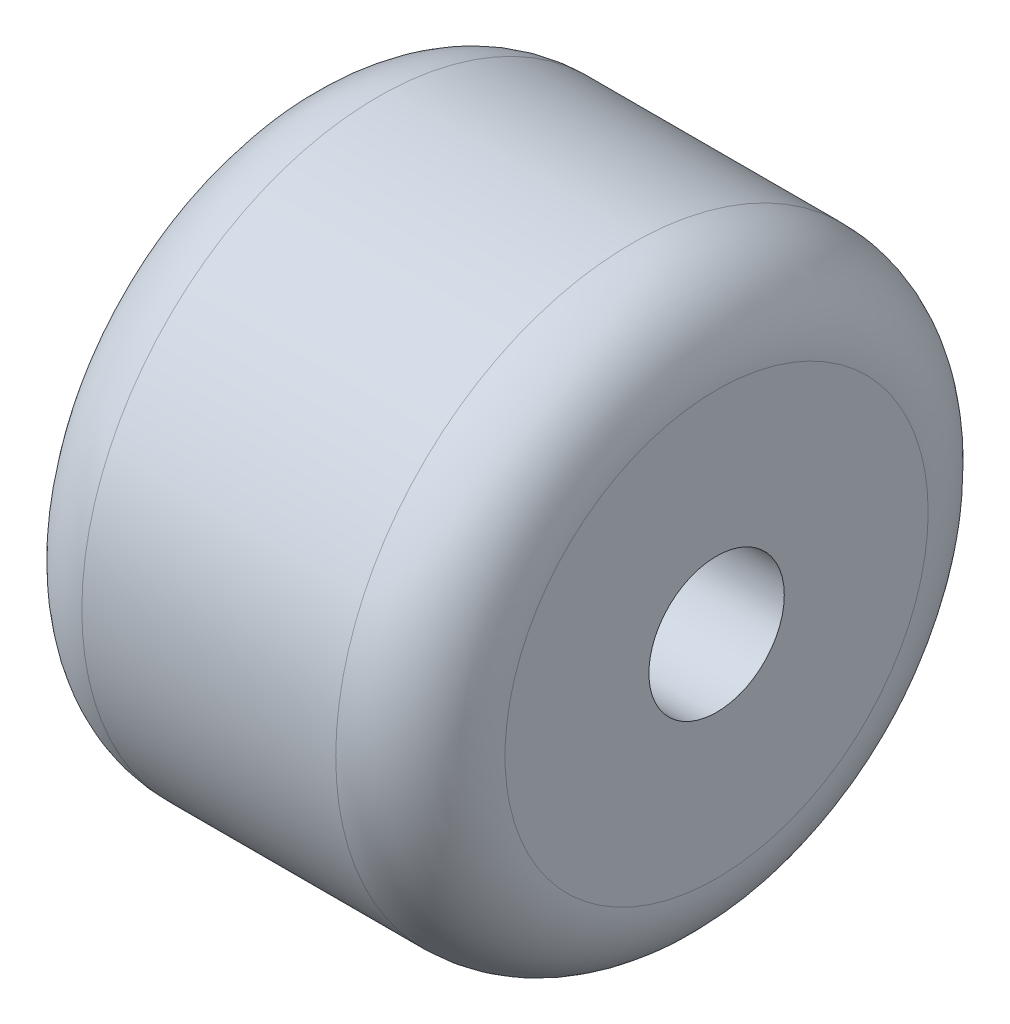
SolidWorks part; units mm, degrees
ref_plane "Plan de face" through (0, 0, 0) normal (0, 0, 1) x (1, 0, 0)
ref_plane "Plan de dessus" through (0, 0, 0) normal (0, 1, 0) x (1, 0, 0)
ref_plane "Plan de droite" through (0, 0, 0) normal (1, 0, 0) x (0, 0, -1)
sketch "Esquisse1" plane through (0, 0, 0) normal (1, 0, 0) x (0, 0, -1)
  circle A0 centre (0, 0) radius 17.5
  circle A1 centre (0, 0) radius 4
  dimension "D1" = 35
  dimension "D2" = 8
extrude "Boss.-Extru.1" add sketch "Esquisse1" along normal blind 25
fillet "Congé1" radius 5 2 edges at (0, 0, -17.5) (25, 0, -17.5)
